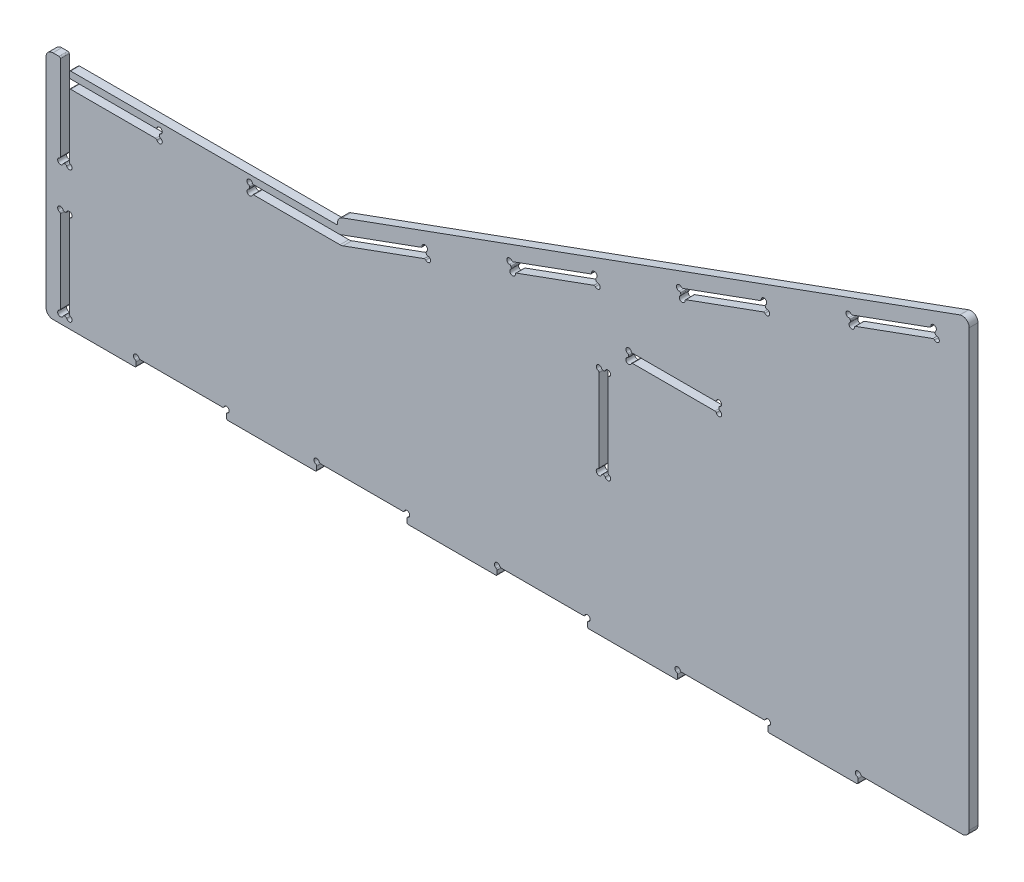
SolidWorks part; units mm, degrees
material "Pine"
ref_plane "Front Plane" through (0, 0, 0) normal (0, 0, 1) x (1, 0, 0)
ref_plane "Top Plane" through (0, 0, 0) normal (0, 1, 0) x (1, 0, 0)
ref_plane "Right Plane" through (0, 0, 0) normal (1, 0, 0) x (0, 0, -1)
sketch "Sketch1" plane through (0, 0, 0) normal (0, 0, 1) x (1, 0, 0)
  line L0 (0, 0) -> (812.8, 0)
  line L1 (0, 0) -> (0, 457.2)
  line L2 (812.8, 0) -> (812.8, 457.2)
  line L3 (0, 457.2) -> (812.8, 457.2)
  dimension "D1" = 812.8
  dimension "D2" = 457.2
extrude "Boss-Extrude1" add sketch "Sketch1" along normal mid plane 6.35
sketch "Sketch4" plane through (0, 0, 3.175) normal (0, 0, 1) x (1, 0, 0)
  line L0 (10, 16.35) -> (675, 16.35)
  line L1 (675, 16.35) -> (675, 341.9565)
  line L2 (675, 341.9565) -> (220, 176.35)
  line L3 (220, 176.35) -> (10, 176.35)
  line L4 (10, 176.35) -> (10, 16.35)
  line L5 (0, 0) -> (812.8, 0) construction
  line L8 (0, 457.2) -> (0, 0) construction
  dimension "D1" = 16.35
  dimension "D2" = 665
  dimension "D3" = 20
  dimension "D4" = 160
  dimension "D5" = 210
  dimension "D6" = 10
extrude "Cut-Extrude3" cut sketch "Sketch4" against normal blind 6.35 flip side to cut
sketch "Sketch5" plane through (0, 0, 3.175) normal (0, 0, 1) x (1, 0, 0)
  line L0 (75, 16.35) -> (10, 16.35)
  line L1 (75, 16.35) -> (75, 10)
  line L2 (10, 16.35) -> (10, 10)
  line L3 (75, 10) -> (10, 10)
  line L4 (10, 16.35) -> (675, 16.35) construction
  dimension "D1" = 6.35
  dimension "D2" = 65
extrude "Boss-Extrude2" add sketch "Sketch5" against normal up to surface (6.35 mm away) up to face at (318, 145.4713, -3.175)
pattern_linear "LPattern2" count 5 spacing 130 along (1, 0, 0) of "Boss-Extrude2"
sketch "Sketch6" plane through (0, 0, 3.175) normal (0, 0, 1) x (1, 0, 0)
  circle A0 centre (75, 16.35) radius 2
  circle A1 centre (140, 16.35) radius 2
  dimension "D1" = 4
extrude "Cut-Extrude4" cut sketch "Sketch6" against normal through all
fillet "Fillet2" radius 1 2 edges at (140, 10, 0) (75, 10, 0)
sketch "Sketch7" plane through (0, 0, 3.175) normal (0, 0, 1) x (1, 0, 0)
  line L7 (140, 14.35) -> (140, 11) construction
  line L8 (77, 16.35) -> (138, 16.35) construction
  line L9 (75, 11) -> (75, 14.35) construction
  line L10 (140, 13.5216) -> (140, 11)
  line L11 (77.8284, 16.35) -> (137.1716, 16.35)
  line L12 (75, 11) -> (75, 13.5216)
  line L13 (141, 10) -> (74, 10)
  arc A12 (140, 11) -> (141, 10) centre (141, 11) ccw construction
  arc A13 (140, 14.35) -> (138, 16.35) centre (140, 16.35) ccw construction
  arc A14 (77, 16.35) -> (75, 14.35) centre (75, 16.35) ccw construction
  arc A15 (74, 10) -> (75, 11) centre (74, 11) ccw construction
  arc A16 (140, 11) -> (141, 10) centre (141, 11) ccw
  arc A17 (140.6667, 14.4644) -> (138.1144, 17.0167) centre (140, 16.35) ccw
  arc A18 (76.8856, 17.0167) -> (74.3333, 14.4644) centre (75, 16.35) ccw
  arc A19 (74, 10) -> (75, 11) centre (74, 11) ccw
  arc A20 (140, 13.5216) -> (140.6667, 14.4644) centre (141, 13.5216) cw
  arc A21 (138.1144, 17.0167) -> (137.1716, 16.35) centre (137.1716, 17.35) cw
  arc A22 (77.8284, 16.35) -> (76.8856, 17.0167) centre (77.8284, 17.35) cw
  arc A23 (74.3333, 14.4644) -> (75, 13.5216) centre (74, 13.5216) cw
  dimension "D1" = 1
extrude "Cut-Extrude5" cut sketch "Sketch7" against normal through all
pattern_linear "LPattern3" count 4 spacing 130 along (1, 0, 0) of "Cut-Extrude5"
sketch "Sketch18" plane through (0, 0, 3.175) normal (0, 0, 1) x (1, 0, 0)
  circle A0 centre (595, 16.35) radius 2
  dimension "D1" = 4
extrude "Cut-Extrude13" cut sketch "Sketch18" against normal through all
fillet "Fillet8" radius 1 3 edges at (597, 16.35, 0) (595, 14.35, 0) (595, 10, 0)
sketch "Sketch10" plane through (0, 0, 3.175) normal (0, 0, 1) x (1, 0, 0)
  line L0 (20.4133, 80.35) -> (20.4133, 21.35) construction
  line L1 (20.4133, 21.35) -> (26.7633, 21.35) construction
  line L2 (26.7633, 21.35) -> (26.7633, 80.35) construction
  line L3 (26.7633, 80.35) -> (20.4133, 80.35) construction
  line L4 (26.7633, 112.35) -> (26.7633, 171.35) construction
  line L5 (26.7633, 171.35) -> (20.4133, 171.35) construction
  line L6 (20.4133, 171.35) -> (20.4133, 112.35) construction
  line L7 (20.4133, 112.35) -> (26.7633, 112.35) construction
  line L8 (20.4133, 176.35) -> (26.7633, 176.35) construction
  line L9 (26.7633, 111.35) -> (20.4133, 111.35) construction
  line L10 (20.4133, 81.35) -> (26.7633, 81.35) construction
  line L11 (26.7633, 16.35) -> (20.4133, 16.35) construction
  line L12 (20.4133, 80.35) -> (20.4133, 21.35) construction
  line L13 (20.4133, 21.35) -> (26.7633, 21.35) construction
  line L14 (26.7633, 21.35) -> (26.7633, 80.35) construction
  line L15 (26.7633, 80.35) -> (20.4133, 80.35) construction
  line L16 (26.7633, 112.35) -> (26.7633, 160) construction
  line L17 (26.7633, 171.35) -> (20.4133, 171.35) construction
  line L18 (20.4133, 171.35) -> (20.4133, 112.35) construction
  line L19 (20.4133, 112.35) -> (26.7633, 112.35) construction
  line L20 (20.4133, 176.35) -> (26.7633, 176.35) construction
  line L21 (26.7633, 111.35) -> (20.4133, 111.35) construction
  line L22 (20.4133, 81.35) -> (26.7633, 81.35) construction
  line L23 (26.7633, 16.35) -> (20.4133, 16.35) construction
  line L28 (90.7633, 166.35) -> (31.7633, 166.35) construction
  line L29 (31.7633, 166.35) -> (31.7633, 160) construction
  line L30 (31.7633, 160) -> (90.7633, 160) construction
  line L31 (90.7633, 160) -> (90.7633, 166.35) construction
  line L32 (221.7633, 166.35) -> (221.7633, 160) construction
  line L34 (91.7633, 166.35) -> (91.7633, 160) construction
  line L35 (156.7633, 160) -> (156.7633, 166.35) construction
  line L40 (90.7633, 166.35) -> (31.7633, 166.35) construction
  line L41 (31.7633, 166.35) -> (31.7633, 160) construction
  line L42 (31.7633, 160) -> (90.7633, 160) construction
  line L43 (90.7633, 160) -> (90.7633, 166.35) construction
  line L44 (221.7633, 166.35) -> (221.7633, 160) construction
  line L45 (156.7633, 160) -> (156.7633, 166.35) construction
  line L46 (91.7633, 166.35) -> (91.7633, 160) construction
  line L48 (591.3549, 294.1128) -> (646.7968, 314.292) construction
  line L49 (646.7968, 314.292) -> (644.6249, 320.2591) construction
  line L50 (644.6249, 320.2591) -> (589.1831, 300.0799) construction
  line L51 (589.1831, 300.0799) -> (591.3549, 294.1128) construction
  line L52 (526.2237, 277.1645) -> (467.023, 255.6173) construction
  line L53 (467.023, 255.6173) -> (469.1949, 249.6502) construction
  line L54 (469.1949, 249.6502) -> (528.3955, 271.1975) construction
  line L55 (528.3955, 271.1975) -> (526.2237, 277.1645) construction
  line L68 (649.3234, 321.9692) -> (651.4952, 316.0021) construction
  line L69 (590.4152, 293.7708) -> (588.2434, 299.7379) construction
  line L70 (527.1634, 277.5065) -> (529.3352, 271.5395) construction
  line L71 (468.2552, 249.3082) -> (466.0834, 255.2752) construction
  line L77 (157.7633, 160) -> (216.7633, 160)
  line L78 (591.3549, 294.1128) -> (646.7968, 314.292) construction
  line L79 (646.7968, 314.292) -> (644.6249, 320.2591) construction
  line L80 (644.6249, 320.2591) -> (589.1831, 300.0799) construction
  line L81 (589.1831, 300.0799) -> (591.3549, 294.1128) construction
  line L82 (526.2237, 277.1645) -> (467.023, 255.6173) construction
  line L83 (467.023, 255.6173) -> (469.1949, 249.6502) construction
  line L84 (469.1949, 249.6502) -> (528.3955, 271.1975) construction
  line L85 (528.3955, 271.1975) -> (526.2237, 277.1645) construction
  line L98 (649.3234, 321.9692) -> (651.4952, 316.0021) construction
  line L99 (590.4152, 293.7708) -> (588.2434, 299.7379) construction
  line L100 (527.1634, 277.5065) -> (529.3352, 271.5395) construction
  line L101 (468.2552, 249.3082) -> (466.0834, 255.2752) construction
  line L102 (216.7633, 160) -> (216.7633, 166.35)
  line L103 (216.7633, 166.35) -> (157.7633, 166.35)
  line L104 (157.7633, 166.35) -> (157.7633, 160)
  line L105 (157.7633, 160) -> (216.7633, 160) construction
  line L106 (216.7633, 160) -> (216.7633, 166.35) construction
  line L107 (216.7633, 166.35) -> (157.7633, 166.35) construction
  line L108 (20.4133, 16.35) -> (26.7633, 16.35)
  line L109 (20.4133, 16.35) -> (20.4133, 81.35)
  line L110 (26.7633, 16.35) -> (26.7633, 81.35)
  line L111 (20.4133, 81.35) -> (26.7633, 81.35)
  line L112 (20.4133, 176.35) -> (20.4133, 111.35)
  line L113 (20.4133, 176.35) -> (26.7633, 176.35)
  line L114 (20.4133, 111.35) -> (26.7633, 111.35)
  line L115 (26.7633, 176.35) -> (26.7633, 166.35)
  line L116 (26.7633, 166.35) -> (91.7633, 166.35)
  line L118 (91.7633, 166.35) -> (91.7633, 160)
  line L119 (26.7633, 160) -> (91.7633, 160)
  line L136 (466.0834, 255.2752) -> (468.2552, 249.3082)
  line L137 (466.0834, 255.2752) -> (527.1634, 277.5065)
  line L138 (468.2552, 249.3082) -> (529.3352, 271.5395)
  line L139 (527.1634, 277.5065) -> (529.3352, 271.5395)
  line L140 (588.2434, 299.7379) -> (590.4152, 293.7708)
  line L141 (588.2434, 299.7379) -> (649.3234, 321.9692)
  line L142 (590.4152, 293.7708) -> (651.4952, 316.0021)
  line L143 (649.3234, 321.9692) -> (651.4952, 316.0021)
  line L144 (26.7633, 166.35) -> (26.7633, 171.35) construction
  line L145 (26.7633, 160) -> (26.7633, 111.35)
  line L146 (157.7633, 166.35) -> (157.7633, 160) construction
  line L147 (406.2355, 226.7349) -> (404.0636, 232.7019) construction
  line L148 (404.0636, 232.7019) -> (344.863, 211.1546) construction
  line L149 (344.863, 211.1546) -> (347.0348, 205.1876) construction
  line L150 (347.0348, 205.1876) -> (406.2355, 226.7349) construction
  line L151 (281.9036, 188.2393) -> (226.4617, 168.0601) construction
  line L152 (226.4617, 168.0601) -> (228.6336, 162.0931) construction
  line L153 (228.6336, 162.0931) -> (284.0754, 182.2722) construction
  line L154 (284.0754, 182.2722) -> (281.9036, 188.2393) construction
  line L155 (407.1752, 227.0769) -> (405.0033, 233.0439) construction
  line L156 (346.0951, 204.8456) -> (343.9233, 210.8126) construction
  line L157 (285.0151, 182.6143) -> (282.8433, 188.5813) construction
  line L158 (223.9351, 160.383) -> (221.7633, 166.35) construction
  line L159 (406.2355, 226.7349) -> (404.0636, 232.7019) construction
  line L160 (404.0636, 232.7019) -> (344.863, 211.1546) construction
  line L161 (344.863, 211.1546) -> (347.0348, 205.1876) construction
  line L162 (347.0348, 205.1876) -> (406.2355, 226.7349) construction
  line L163 (281.9036, 188.2393) -> (226.4617, 168.0601) construction
  line L164 (226.4617, 168.0601) -> (228.6336, 162.0931) construction
  line L165 (228.6336, 162.0931) -> (284.0754, 182.2722) construction
  line L166 (284.0754, 182.2722) -> (281.9036, 188.2393) construction
  line L167 (407.1752, 227.0769) -> (405.0033, 233.0439) construction
  line L168 (346.0951, 204.8456) -> (343.9233, 210.8126) construction
  line L169 (285.0151, 182.6143) -> (282.8433, 188.5813) construction
  line L170 (223.9351, 160.383) -> (221.7633, 166.35) construction
  line L171 (343.9233, 210.8126) -> (346.0951, 204.8456)
  line L172 (343.9233, 210.8126) -> (405.0033, 233.0439)
  line L173 (346.0951, 204.8456) -> (407.1752, 227.0769)
  line L174 (405.0033, 233.0439) -> (407.1752, 227.0769)
  line L175 (156.7633, 160) -> (221.7633, 160)
  line L176 (223.9351, 160.383) -> (285.0151, 182.6143)
  line L177 (156.7633, 166.35) -> (156.7633, 160)
  line L178 (282.8433, 188.5813) -> (285.0151, 182.6143)
  line L179 (282.8433, 188.5813) -> (221.7633, 166.35)
  line L180 (221.7633, 166.35) -> (156.7633, 166.35)
  arc A1 (221.7633, 160) -> (223.9351, 160.383) centre (221.7633, 166.35) ccw
  dimension "D1" = 0
extrude "Cut-Extrude7" cut sketch "Sketch10" against normal through all
sketch "Sketch11" plane through (0, 0, 3.175) normal (0, 0, 1) x (1, 0, 0)
  circle A0 centre (20.4133, 16.35) radius 2
  circle A1 centre (26.7633, 16.35) radius 2
  circle A2 centre (26.7633, 81.35) radius 2
  circle A3 centre (20.4133, 81.35) radius 2
  circle A4 centre (20.4133, 111.35) radius 2
  circle A5 centre (26.7633, 111.35) radius 2
  circle A6 centre (91.7633, 160) radius 2
  circle A7 centre (91.7633, 166.35) radius 2
  circle A8 centre (156.7633, 166.35) radius 2
  circle A9 centre (156.7633, 160) radius 2
  circle A11 centre (282.8433, 188.5813) radius 2
  circle A12 centre (285.0151, 182.6143) radius 2
  dimension "D1" = 4
extrude "Cut-Extrude8" cut sketch "Sketch11" against normal through all
sketch "Sketch19" plane through (0, 0, 3.175) normal (0, 0, 1) x (1, 0, 0)
  line L0 (220, 176.35) -> (220, 171.35)
  line L1 (220, 176.35) -> (26.7633, 176.35)
  line L2 (220, 171.35) -> (26.7633, 171.35)
  line L3 (26.7633, 176.35) -> (26.7633, 171.35)
  line L5 (26.7633, 166.35) -> (26.7633, 176.35) construction
  point P0 (26.7633, 168.9047)
  dimension "D1" = 5
extrude "Cut-Extrude14" cut sketch "Sketch19" against normal through all
fillet "Fillet4" radius 1 30 edges at (89.7633, 160, 0) (89.7633, 166.35, 0) (91.7633, 164.35, 0) (91.7633, 162, 0) (26.7633, 166.35, 0) (26.7633, 160, 0) (20.4133, 176.35, 0) (26.7633, 113.35, 0) (20.4133, 113.35, 0) (24.7633, 111.35, 0) (22.4133, 111.35, 0) (20.4133, 79.35, 0) (22.4133, 81.35, 0) (24.7633, 81.35, 0) (26.7633, 79.35, 0) (26.7633, 18.35, 0) (24.7633, 16.35, 0) (22.4133, 16.35, 0) (20.4133, 18.35, 0) (283.1357, 181.9302, 0) (284.3311, 184.4936, 0) (283.5273, 186.7019, 0) (280.9639, 187.8973, 0) (221.7633, 166.35, 0) (158.7633, 166.35, 0) (156.7633, 164.35, 0) (156.7633, 162, 0) (158.7633, 160, 0) (220, 171.35, 0) (26.7633, 171.35, 0)
sketch "Sketch12" plane through (0, 0, 3.175) normal (0, 0, 1) x (1, 0, 0)
  circle A0 centre (588.2434, 299.7379) radius 2
  circle A1 centre (590.4152, 293.7708) radius 2
  circle A2 centre (649.3234, 321.9692) radius 2
  circle A3 centre (651.4952, 316.0021) radius 2
  dimension "D1" = 4
extrude "Cut-Extrude9" cut sketch "Sketch12" against normal through all
sketch "Sketch13" plane through (0, 0, 3.175) normal (0, 0, 1) x (1, 0, 0)
  line L0 (592.2946, 294.4548) -> (649.6159, 315.3181) construction
  line L1 (650.8112, 317.8815) -> (650.0075, 320.0898) construction
  line L2 (647.444, 321.2851) -> (590.1228, 300.4219) construction
  line L3 (588.9274, 297.8585) -> (589.7312, 295.6502) construction
  line L4 (593.0731, 294.7382) -> (648.8374, 315.0347)
  line L5 (650.5279, 318.66) -> (650.2908, 319.3113)
  line L6 (646.6656, 321.0018) -> (590.9012, 300.7052)
  line L7 (589.2108, 297.08) -> (589.4478, 296.4287)
  circle A0 centre (590.4152, 293.7708) radius 2 construction
  arc A1 (649.6159, 315.3181) -> (650.8112, 317.8815) centre (651.4952, 316.0021) ccw construction
  arc A2 (650.0075, 320.0898) -> (647.444, 321.2851) centre (649.3234, 321.9692) ccw construction
  circle A3 centre (588.2434, 299.7379) radius 2 construction
  arc A4 (589.1438, 295.3147) -> (592.4151, 293.7893) centre (590.4152, 293.7708) ccw
  arc A5 (649.9514, 314.7307) -> (651.4768, 318.002) centre (651.4952, 316.0021) ccw
  arc A6 (650.5948, 320.4253) -> (647.3235, 321.9507) centre (649.3234, 321.9692) ccw
  arc A7 (589.7873, 301.0092) -> (588.2618, 297.7379) centre (588.2434, 299.7379) ccw
  arc A8 (646.6656, 321.0018) -> (647.3235, 321.9507) centre (646.3235, 321.9415) ccw
  arc A9 (650.5948, 320.4253) -> (650.2908, 319.3113) centre (651.2305, 319.6533) ccw
  arc A10 (650.5279, 318.66) -> (651.4768, 318.002) centre (651.4676, 319.002) ccw
  arc A11 (649.9514, 314.7307) -> (648.8374, 315.0347) centre (649.1794, 314.095) ccw
  arc A12 (593.0731, 294.7382) -> (592.4151, 293.7893) centre (593.4151, 293.7985) ccw
  arc A13 (590.9012, 300.7052) -> (589.7873, 301.0092) centre (590.5592, 301.6449) cw
  arc A14 (588.2618, 297.7379) -> (589.2108, 297.08) centre (588.2711, 296.738) cw
  arc A15 (589.4478, 296.4287) -> (589.1438, 295.3147) centre (588.5081, 296.0866) cw
  dimension "D1" = 1
extrude "Cut-Extrude10" cut sketch "Sketch13" against normal through all
pattern_linear "LPattern4" count 3 spacing 130 along (-0.9397, -0.342, 0) of "Cut-Extrude10"
sketch "Sketch14" plane through (0, 0, 3.175) normal (0, 0, 1) x (1, 0, 0)
  line L0 (408.3566, 176.35) -> (414.7066, 176.35)
  line L1 (408.3566, 176.35) -> (408.3566, 111.35)
  line L2 (414.7066, 176.35) -> (414.7066, 111.35)
  line L3 (408.3566, 111.35) -> (414.7066, 111.35)
  line L4 (429.7066, 197.7) -> (429.7066, 191.35)
  line L5 (429.7066, 197.7) -> (494.7066, 197.7)
  line L6 (429.7066, 191.35) -> (494.7066, 191.35)
  line L7 (494.7066, 197.7) -> (494.7066, 191.35)
  line L8 (14.7066, 176.35) -> (14.7066, 16.35) construction
  line L9 (19.4133, 176.35) -> (10, 176.35) construction
  line L11 (429.7066, 191.35) -> (414.7066, 191.35) construction
  line L12 (414.7066, 176.35) -> (414.7066, 191.35) construction
  line L13 (19.4133, 176.35) -> (10, 176.35) construction
  line L15 (77.8284, 16.35) -> (137.1716, 16.35) construction
  dimension "D1" = 6.35
  dimension "D2" = 65
  dimension "D3" = 400
  dimension "D5" = 15
  dimension "D6" = 15
extrude "Cut-Extrude11" cut sketch "Sketch14" against normal through all
sketch "Sketch15" plane through (0, 0, 3.175) normal (0, 0, 1) x (1, 0, 0)
  circle A0 centre (408.3566, 176.35) radius 2
  circle A1 centre (414.7066, 176.35) radius 2
  circle A2 centre (408.3566, 111.35) radius 2
  circle A3 centre (414.7066, 111.35) radius 2
  circle A4 centre (429.7066, 197.7) radius 2
  circle A5 centre (429.7066, 191.35) radius 2
  circle A6 centre (494.7066, 191.35) radius 2
  circle A7 centre (494.7066, 197.7) radius 2
  dimension "D1" = 4
extrude "Cut-Extrude12" cut sketch "Sketch15" against normal through all
fillet "Fillet7" radius 1 16 edges at (492.7066, 197.7, 0) (494.7066, 195.7, 0) (494.7066, 193.35, 0) (492.7066, 191.35, 0) (431.7066, 191.35, 0) (431.7066, 197.7, 0) (429.7066, 195.7, 0) (429.7066, 193.35, 0) (408.3566, 174.35, 0) (410.3566, 176.35, 0) (412.7066, 176.35, 0) (414.7066, 174.35, 0) (414.7066, 113.35, 0) (412.7066, 111.35, 0) (410.3566, 111.35, 0) (408.3566, 113.35, 0)
fillet "Fillet9" radius 5 5 edges at (675, 16.35, 0) (675, 341.9565, 0) (10, 176.35, 0) (10, 10, 0) (220, 176.35, 0)
